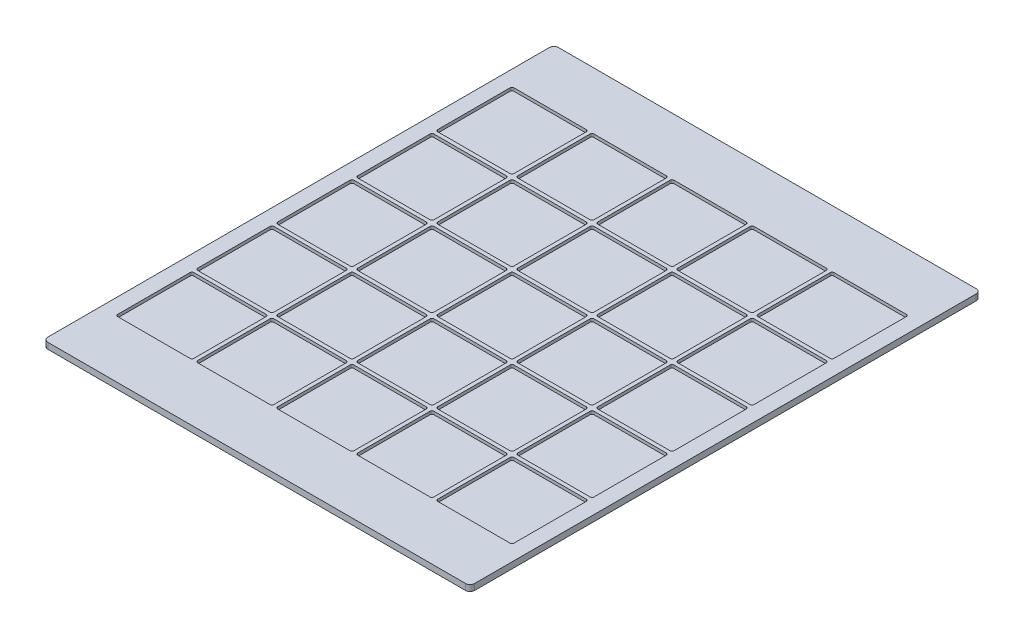
SolidWorks part; units mm, degrees
ref_plane "Front Plane" through (0, 0, 0) normal (0, 0, 1) x (1, 0, 0)
ref_plane "Top Plane" through (0, 0, 0) normal (0, 1, 0) x (1, 0, 0)
ref_plane "Right Plane" through (0, 0, 0) normal (1, 0, 0) x (0, 0, -1)
sketch "Sketch1" plane through (0, 0, 0) normal (0, 1, 0) x (1, 0, 0)
  line L0 (-193.675, 203.2) -> (-73.025, 203.2)
  line L1 (-327.025, 203.2) -> (-206.375, 203.2)
  line L2 (-330.2, 206.375) -> (-330.2, 327.025)
  line L3 (-327.025, 330.2) -> (-206.375, 330.2)
  line L4 (-203.2, 206.375) -> (-203.2, 327.025)
  line L5 (-330.2, 203.2) -> (-203.2, 330.2) construction
  line L6 (-330.2, 330.2) -> (-203.2, 203.2) construction
  line L7 (-196.85, 206.375) -> (-196.85, 327.025)
  line L8 (-193.675, 330.2) -> (-73.025, 330.2)
  line L9 (-69.85, 206.375) -> (-69.85, 327.025)
  line L10 (-196.85, 203.2) -> (-69.85, 330.2) construction
  line L11 (-196.85, 330.2) -> (-69.85, 203.2) construction
  line L12 (-60.325, 203.2) -> (60.325, 203.2)
  line L13 (-63.5, 206.375) -> (-63.5, 327.025)
  line L14 (-60.325, 330.2) -> (60.325, 330.2)
  line L15 (63.5, 206.375) -> (63.5, 327.025)
  line L16 (-63.5, 203.2) -> (63.5, 330.2) construction
  line L17 (-63.5, 330.2) -> (63.5, 203.2) construction
  line L18 (73.025, 203.2) -> (193.675, 203.2)
  line L19 (69.85, 206.375) -> (69.85, 327.025)
  line L20 (73.025, 330.2) -> (193.675, 330.2)
  line L21 (196.85, 206.375) -> (196.85, 327.025)
  line L22 (69.85, 203.2) -> (196.85, 330.2) construction
  line L23 (69.85, 330.2) -> (196.85, 203.2) construction
  line L24 (206.375, 203.2) -> (327.025, 203.2)
  line L25 (203.2, 206.375) -> (203.2, 327.025)
  line L26 (206.375, 330.2) -> (327.025, 330.2)
  line L27 (330.2, 206.375) -> (330.2, 327.025)
  line L28 (203.2, 203.2) -> (330.2, 330.2) construction
  line L29 (203.2, 330.2) -> (330.2, 203.2) construction
  line L30 (-193.675, 69.85) -> (-73.025, 69.85)
  line L31 (-196.85, 73.025) -> (-196.85, 193.675)
  line L32 (-193.675, 196.85) -> (-73.025, 196.85)
  line L33 (-69.85, 73.025) -> (-69.85, 193.675)
  line L34 (-196.85, 69.85) -> (-69.85, 196.85) construction
  line L35 (-196.85, 196.85) -> (-69.85, 69.85) construction
  line L36 (-60.325, 69.85) -> (60.325, 69.85)
  line L37 (-63.5, 73.025) -> (-63.5, 193.675)
  line L38 (-60.325, 196.85) -> (60.325, 196.85)
  line L39 (63.5, 73.025) -> (63.5, 193.675)
  line L40 (-63.5, 69.85) -> (63.5, 196.85) construction
  line L41 (-63.5, 196.85) -> (63.5, 69.85) construction
  line L42 (73.025, 69.85) -> (193.675, 69.85)
  line L43 (69.85, 73.025) -> (69.85, 193.675)
  line L44 (73.025, 196.85) -> (193.675, 196.85)
  line L45 (196.85, 73.025) -> (196.85, 193.675)
  line L46 (69.85, 69.85) -> (196.85, 196.85) construction
  line L47 (69.85, 196.85) -> (196.85, 69.85) construction
  line L48 (206.375, 69.85) -> (327.025, 69.85)
  line L49 (203.2, 73.025) -> (203.2, 193.675)
  line L50 (206.375, 196.85) -> (327.025, 196.85)
  line L51 (330.2, 73.025) -> (330.2, 193.675)
  line L52 (203.2, 69.85) -> (330.2, 196.85) construction
  line L53 (203.2, 196.85) -> (330.2, 69.85) construction
  line L54 (-193.675, -63.5) -> (-73.025, -63.5)
  line L55 (-196.85, -60.325) -> (-196.85, 60.325)
  line L56 (-193.675, 63.5) -> (-73.025, 63.5)
  line L57 (-69.85, -60.325) -> (-69.85, 60.325)
  line L58 (-196.85, -63.5) -> (-69.85, 63.5) construction
  line L59 (-196.85, 63.5) -> (-69.85, -63.5) construction
  line L60 (-60.325, -63.5) -> (60.325, -63.5)
  line L61 (-63.5, -60.325) -> (-63.5, 60.325)
  line L62 (-60.325, 63.5) -> (60.325, 63.5)
  line L63 (63.5, -60.325) -> (63.5, 60.325)
  line L64 (-63.5, -63.5) -> (63.5, 63.5) construction
  line L65 (-63.5, 63.5) -> (63.5, -63.5) construction
  line L66 (73.025, -63.5) -> (193.675, -63.5)
  line L67 (69.85, -60.325) -> (69.85, 60.325)
  line L68 (73.025, 63.5) -> (193.675, 63.5)
  line L69 (196.85, -60.325) -> (196.85, 60.325)
  line L70 (69.85, -63.5) -> (196.85, 63.5) construction
  line L71 (69.85, 63.5) -> (196.85, -63.5) construction
  line L72 (206.375, -63.5) -> (327.025, -63.5)
  line L73 (203.2, -60.325) -> (203.2, 60.325)
  line L74 (206.375, 63.5) -> (327.025, 63.5)
  line L75 (330.2, -60.325) -> (330.2, 60.325)
  line L76 (203.2, -63.5) -> (330.2, 63.5) construction
  line L77 (203.2, 63.5) -> (330.2, -63.5) construction
  line L78 (-193.675, -196.85) -> (-73.025, -196.85)
  line L79 (-196.85, -193.675) -> (-196.85, -73.025)
  line L80 (-193.675, -69.85) -> (-73.025, -69.85)
  line L81 (-69.85, -193.675) -> (-69.85, -73.025)
  line L82 (-196.85, -196.85) -> (-69.85, -69.85) construction
  line L83 (-196.85, -69.85) -> (-69.85, -196.85) construction
  line L84 (-60.325, -196.85) -> (60.325, -196.85)
  line L85 (-63.5, -193.675) -> (-63.5, -73.025)
  line L86 (-60.325, -69.85) -> (60.325, -69.85)
  line L87 (63.5, -193.675) -> (63.5, -73.025)
  line L88 (-63.5, -196.85) -> (63.5, -69.85) construction
  line L89 (-63.5, -69.85) -> (63.5, -196.85) construction
  line L90 (73.025, -196.85) -> (193.675, -196.85)
  line L91 (69.85, -193.675) -> (69.85, -73.025)
  line L92 (73.025, -69.85) -> (193.675, -69.85)
  line L93 (196.85, -193.675) -> (196.85, -73.025)
  line L94 (69.85, -196.85) -> (196.85, -69.85) construction
  line L95 (69.85, -69.85) -> (196.85, -196.85) construction
  line L96 (206.375, -196.85) -> (327.025, -196.85)
  line L97 (203.2, -193.675) -> (203.2, -73.025)
  line L98 (206.375, -69.85) -> (327.025, -69.85)
  line L99 (330.2, -193.675) -> (330.2, -73.025)
  line L100 (203.2, -196.85) -> (330.2, -69.85) construction
  line L101 (203.2, -69.85) -> (330.2, -196.85) construction
  line L102 (-193.675, -330.2) -> (-73.025, -330.2)
  line L103 (-196.85, -327.025) -> (-196.85, -206.375)
  line L104 (-193.675, -203.2) -> (-73.025, -203.2)
  line L105 (-69.85, -327.025) -> (-69.85, -206.375)
  line L106 (-196.85, -330.2) -> (-69.85, -203.2) construction
  line L107 (-196.85, -203.2) -> (-69.85, -330.2) construction
  line L108 (-60.325, -330.2) -> (60.325, -330.2)
  line L109 (-63.5, -327.025) -> (-63.5, -206.375)
  line L110 (-60.325, -203.2) -> (60.325, -203.2)
  line L111 (63.5, -327.025) -> (63.5, -206.375)
  line L112 (-63.5, -330.2) -> (63.5, -203.2) construction
  line L113 (-63.5, -203.2) -> (63.5, -330.2) construction
  line L114 (73.025, -330.2) -> (193.675, -330.2)
  line L115 (69.85, -327.025) -> (69.85, -206.375)
  line L116 (73.025, -203.2) -> (193.675, -203.2)
  line L117 (196.85, -327.025) -> (196.85, -206.375)
  line L118 (69.85, -330.2) -> (196.85, -203.2) construction
  line L119 (69.85, -203.2) -> (196.85, -330.2) construction
  line L120 (206.375, -330.2) -> (327.025, -330.2)
  line L121 (203.2, -327.025) -> (203.2, -206.375)
  line L122 (206.375, -203.2) -> (327.025, -203.2)
  line L123 (330.2, -327.025) -> (330.2, -206.375)
  line L124 (203.2, -330.2) -> (330.2, -203.2) construction
  line L125 (203.2, -203.2) -> (330.2, -330.2) construction
  line L126 (-327.025, 69.85) -> (-206.375, 69.85)
  line L127 (-330.2, 73.025) -> (-330.2, 193.675)
  line L128 (-327.025, 196.85) -> (-206.375, 196.85)
  line L129 (-203.2, 73.025) -> (-203.2, 193.675)
  line L130 (-330.2, 69.85) -> (-203.2, 196.85) construction
  line L131 (-330.2, 196.85) -> (-203.2, 69.85) construction
  line L132 (-327.025, -63.5) -> (-206.375, -63.5)
  line L133 (-330.2, -60.325) -> (-330.2, 60.325)
  line L134 (-327.025, 63.5) -> (-206.375, 63.5)
  line L135 (-203.2, -60.325) -> (-203.2, 60.325)
  line L136 (-330.2, -63.5) -> (-203.2, 63.5) construction
  line L137 (-330.2, 63.5) -> (-203.2, -63.5) construction
  line L138 (-327.025, -196.85) -> (-206.375, -196.85)
  line L139 (-330.2, -193.675) -> (-330.2, -73.025)
  line L140 (-327.025, -69.85) -> (-206.375, -69.85)
  line L141 (-203.2, -193.675) -> (-203.2, -73.025)
  line L142 (-330.2, -196.85) -> (-203.2, -69.85) construction
  line L143 (-330.2, -69.85) -> (-203.2, -196.85) construction
  line L144 (-327.025, -330.2) -> (-206.375, -330.2)
  line L145 (-330.2, -327.025) -> (-330.2, -206.375)
  line L146 (-327.025, -203.2) -> (-206.375, -203.2)
  line L147 (-203.2, -327.025) -> (-203.2, -206.375)
  line L148 (-330.2, -330.2) -> (-203.2, -203.2) construction
  line L149 (-330.2, -203.2) -> (-203.2, -330.2) construction
  line L151 (-355.6, 425.45) -> (355.6, 425.45)
  line L152 (-355.6, 425.45) -> (-355.6, -425.45)
  line L153 (-355.6, -425.45) -> (355.6, -425.45)
  line L154 (355.6, 425.45) -> (355.6, -425.45)
  arc A0 (-206.375, 330.2) -> (-203.2, 327.025) centre (-206.375, 327.025) cw
  arc A1 (-206.375, 203.2) -> (-203.2, 206.375) centre (-206.375, 206.375) ccw
  arc A2 (-327.025, 203.2) -> (-330.2, 206.375) centre (-327.025, 206.375) cw
  arc A3 (-330.2, 327.025) -> (-327.025, 330.2) centre (-327.025, 327.025) cw
  arc A4 (-73.025, 330.2) -> (-69.85, 327.025) centre (-73.025, 327.025) cw
  arc A5 (-73.025, 203.2) -> (-69.85, 206.375) centre (-73.025, 206.375) ccw
  arc A6 (-193.675, 203.2) -> (-196.85, 206.375) centre (-193.675, 206.375) cw
  arc A7 (-196.85, 327.025) -> (-193.675, 330.2) centre (-193.675, 327.025) cw
  arc A8 (60.325, 330.2) -> (63.5, 327.025) centre (60.325, 327.025) cw
  arc A9 (60.325, 203.2) -> (63.5, 206.375) centre (60.325, 206.375) ccw
  arc A10 (-60.325, 203.2) -> (-63.5, 206.375) centre (-60.325, 206.375) cw
  arc A11 (-63.5, 327.025) -> (-60.325, 330.2) centre (-60.325, 327.025) cw
  arc A12 (193.675, 330.2) -> (196.85, 327.025) centre (193.675, 327.025) cw
  arc A13 (193.675, 203.2) -> (196.85, 206.375) centre (193.675, 206.375) ccw
  arc A14 (73.025, 203.2) -> (69.85, 206.375) centre (73.025, 206.375) cw
  arc A15 (69.85, 327.025) -> (73.025, 330.2) centre (73.025, 327.025) cw
  arc A16 (327.025, 330.2) -> (330.2, 327.025) centre (327.025, 327.025) cw
  arc A17 (327.025, 203.2) -> (330.2, 206.375) centre (327.025, 206.375) ccw
  arc A18 (206.375, 203.2) -> (203.2, 206.375) centre (206.375, 206.375) cw
  arc A19 (203.2, 327.025) -> (206.375, 330.2) centre (206.375, 327.025) cw
  arc A20 (-73.025, 196.85) -> (-69.85, 193.675) centre (-73.025, 193.675) cw
  arc A21 (-73.025, 69.85) -> (-69.85, 73.025) centre (-73.025, 73.025) ccw
  arc A22 (-193.675, 69.85) -> (-196.85, 73.025) centre (-193.675, 73.025) cw
  arc A23 (-196.85, 193.675) -> (-193.675, 196.85) centre (-193.675, 193.675) cw
  arc A24 (60.325, 196.85) -> (63.5, 193.675) centre (60.325, 193.675) cw
  arc A25 (60.325, 69.85) -> (63.5, 73.025) centre (60.325, 73.025) ccw
  arc A26 (-60.325, 69.85) -> (-63.5, 73.025) centre (-60.325, 73.025) cw
  arc A27 (-63.5, 193.675) -> (-60.325, 196.85) centre (-60.325, 193.675) cw
  arc A28 (193.675, 196.85) -> (196.85, 193.675) centre (193.675, 193.675) cw
  arc A29 (193.675, 69.85) -> (196.85, 73.025) centre (193.675, 73.025) ccw
  arc A30 (73.025, 69.85) -> (69.85, 73.025) centre (73.025, 73.025) cw
  arc A31 (69.85, 193.675) -> (73.025, 196.85) centre (73.025, 193.675) cw
  arc A32 (327.025, 196.85) -> (330.2, 193.675) centre (327.025, 193.675) cw
  arc A33 (327.025, 69.85) -> (330.2, 73.025) centre (327.025, 73.025) ccw
  arc A34 (206.375, 69.85) -> (203.2, 73.025) centre (206.375, 73.025) cw
  arc A35 (203.2, 193.675) -> (206.375, 196.85) centre (206.375, 193.675) cw
  arc A36 (-73.025, 63.5) -> (-69.85, 60.325) centre (-73.025, 60.325) cw
  arc A37 (-73.025, -63.5) -> (-69.85, -60.325) centre (-73.025, -60.325) ccw
  arc A38 (-193.675, -63.5) -> (-196.85, -60.325) centre (-193.675, -60.325) cw
  arc A39 (-196.85, 60.325) -> (-193.675, 63.5) centre (-193.675, 60.325) cw
  arc A40 (60.325, 63.5) -> (63.5, 60.325) centre (60.325, 60.325) cw
  arc A41 (60.325, -63.5) -> (63.5, -60.325) centre (60.325, -60.325) ccw
  arc A42 (-60.325, -63.5) -> (-63.5, -60.325) centre (-60.325, -60.325) cw
  arc A43 (-63.5, 60.325) -> (-60.325, 63.5) centre (-60.325, 60.325) cw
  arc A44 (193.675, 63.5) -> (196.85, 60.325) centre (193.675, 60.325) cw
  arc A45 (193.675, -63.5) -> (196.85, -60.325) centre (193.675, -60.325) ccw
  arc A46 (73.025, -63.5) -> (69.85, -60.325) centre (73.025, -60.325) cw
  arc A47 (69.85, 60.325) -> (73.025, 63.5) centre (73.025, 60.325) cw
  arc A48 (327.025, 63.5) -> (330.2, 60.325) centre (327.025, 60.325) cw
  arc A49 (327.025, -63.5) -> (330.2, -60.325) centre (327.025, -60.325) ccw
  arc A50 (206.375, -63.5) -> (203.2, -60.325) centre (206.375, -60.325) cw
  arc A51 (203.2, 60.325) -> (206.375, 63.5) centre (206.375, 60.325) cw
  arc A52 (-73.025, -69.85) -> (-69.85, -73.025) centre (-73.025, -73.025) cw
  arc A53 (-73.025, -196.85) -> (-69.85, -193.675) centre (-73.025, -193.675) ccw
  arc A54 (-193.675, -196.85) -> (-196.85, -193.675) centre (-193.675, -193.675) cw
  arc A55 (-196.85, -73.025) -> (-193.675, -69.85) centre (-193.675, -73.025) cw
  arc A56 (60.325, -69.85) -> (63.5, -73.025) centre (60.325, -73.025) cw
  arc A57 (60.325, -196.85) -> (63.5, -193.675) centre (60.325, -193.675) ccw
  arc A58 (-60.325, -196.85) -> (-63.5, -193.675) centre (-60.325, -193.675) cw
  arc A59 (-63.5, -73.025) -> (-60.325, -69.85) centre (-60.325, -73.025) cw
  arc A60 (193.675, -69.85) -> (196.85, -73.025) centre (193.675, -73.025) cw
  arc A61 (193.675, -196.85) -> (196.85, -193.675) centre (193.675, -193.675) ccw
  arc A62 (73.025, -196.85) -> (69.85, -193.675) centre (73.025, -193.675) cw
  arc A63 (69.85, -73.025) -> (73.025, -69.85) centre (73.025, -73.025) cw
  arc A64 (327.025, -69.85) -> (330.2, -73.025) centre (327.025, -73.025) cw
  arc A65 (327.025, -196.85) -> (330.2, -193.675) centre (327.025, -193.675) ccw
  arc A66 (206.375, -196.85) -> (203.2, -193.675) centre (206.375, -193.675) cw
  arc A67 (203.2, -73.025) -> (206.375, -69.85) centre (206.375, -73.025) cw
  arc A68 (-73.025, -203.2) -> (-69.85, -206.375) centre (-73.025, -206.375) cw
  arc A69 (-73.025, -330.2) -> (-69.85, -327.025) centre (-73.025, -327.025) ccw
  arc A70 (-193.675, -330.2) -> (-196.85, -327.025) centre (-193.675, -327.025) cw
  arc A71 (-196.85, -206.375) -> (-193.675, -203.2) centre (-193.675, -206.375) cw
  arc A72 (60.325, -203.2) -> (63.5, -206.375) centre (60.325, -206.375) cw
  arc A73 (60.325, -330.2) -> (63.5, -327.025) centre (60.325, -327.025) ccw
  arc A74 (-60.325, -330.2) -> (-63.5, -327.025) centre (-60.325, -327.025) cw
  arc A75 (-63.5, -206.375) -> (-60.325, -203.2) centre (-60.325, -206.375) cw
  arc A76 (193.675, -203.2) -> (196.85, -206.375) centre (193.675, -206.375) cw
  arc A77 (193.675, -330.2) -> (196.85, -327.025) centre (193.675, -327.025) ccw
  arc A78 (73.025, -330.2) -> (69.85, -327.025) centre (73.025, -327.025) cw
  arc A79 (69.85, -206.375) -> (73.025, -203.2) centre (73.025, -206.375) cw
  arc A80 (327.025, -203.2) -> (330.2, -206.375) centre (327.025, -206.375) cw
  arc A81 (327.025, -330.2) -> (330.2, -327.025) centre (327.025, -327.025) ccw
  arc A82 (206.375, -330.2) -> (203.2, -327.025) centre (206.375, -327.025) cw
  arc A83 (203.2, -206.375) -> (206.375, -203.2) centre (206.375, -206.375) cw
  arc A84 (-206.375, 196.85) -> (-203.2, 193.675) centre (-206.375, 193.675) cw
  arc A85 (-206.375, 69.85) -> (-203.2, 73.025) centre (-206.375, 73.025) ccw
  arc A86 (-327.025, 69.85) -> (-330.2, 73.025) centre (-327.025, 73.025) cw
  arc A87 (-330.2, 193.675) -> (-327.025, 196.85) centre (-327.025, 193.675) cw
  arc A88 (-206.375, 63.5) -> (-203.2, 60.325) centre (-206.375, 60.325) cw
  arc A89 (-206.375, -63.5) -> (-203.2, -60.325) centre (-206.375, -60.325) ccw
  arc A90 (-327.025, -63.5) -> (-330.2, -60.325) centre (-327.025, -60.325) cw
  arc A91 (-330.2, 60.325) -> (-327.025, 63.5) centre (-327.025, 60.325) cw
  arc A92 (-206.375, -69.85) -> (-203.2, -73.025) centre (-206.375, -73.025) cw
  arc A93 (-206.375, -196.85) -> (-203.2, -193.675) centre (-206.375, -193.675) ccw
  arc A94 (-327.025, -196.85) -> (-330.2, -193.675) centre (-327.025, -193.675) cw
  arc A95 (-330.2, -73.025) -> (-327.025, -69.85) centre (-327.025, -73.025) cw
  arc A96 (-206.375, -203.2) -> (-203.2, -206.375) centre (-206.375, -206.375) cw
  arc A97 (-206.375, -330.2) -> (-203.2, -327.025) centre (-206.375, -327.025) ccw
  arc A98 (-327.025, -330.2) -> (-330.2, -327.025) centre (-327.025, -327.025) cw
  arc A99 (-330.2, -206.375) -> (-327.025, -203.2) centre (-327.025, -206.375) cw
  point P0 (0, 0)
  point P18 (0, 0)
  point P19 (0, 0)
  point P21 (133.35, 0)
  point P38 (266.7, 0)
  point P55 (400.05, 0)
  point P72 (533.4, 0)
  point P89 (133.35, -133.35)
  point P106 (266.7, -133.35)
  point P123 (400.05, -133.35)
  point P140 (533.4, -133.35)
  point P157 (133.35, -266.7)
  point P174 (266.7, -266.7)
  point P191 (400.05, -266.7)
  point P208 (533.4, -266.7)
  point P225 (133.35, -400.05)
  point P242 (266.7, -400.05)
  point P259 (400.05, -400.05)
  point P276 (533.4, -400.05)
  point P293 (133.35, -533.4)
  point P310 (266.7, -533.4)
  point P327 (400.05, -533.4)
  point P344 (533.4, -533.4)
  point P361 (0, -133.35)
  point P378 (0, -266.7)
  point P395 (0, -400.05)
  point P412 (0, -533.4)
  dimension "D3" = 3.175
  dimension "D1" = 127
  dimension "D2" = 127
  dimension "D6" = 95.25
  dimension "D7" = 25.4
  dimension "D8" = 25.4
  dimension "D9" = 95.25
  dimension "D11" = 6.35
  dimension "D12" = 6.35
  dimension "D4" = 5
  dimension "D5" = 5
extrude "Boss-Extrude1" add sketch "Sketch1" along normal blind 5.08
sketch "Sketch2" plane through (0, 0, 0) normal (0, -1, 0) x (1, 0, 0)
  line L0 (-355.6, 425.45) -> (355.6, 425.45) construction
  line L1 (-355.6, -425.45) -> (-355.6, 425.45) construction
  line L2 (-355.6, 425.45) -> (355.6, 425.45)
  line L3 (-355.6, -425.45) -> (-355.6, 425.45)
  line L4 (-355.6, -425.45) -> (355.6, -425.45) construction
  line L5 (-355.6, -425.45) -> (355.6, -425.45)
  line L6 (355.6, -425.45) -> (355.6, 425.45) construction
  line L7 (355.6, -425.45) -> (355.6, 425.45)
extrude "Boss-Extrude2" add sketch "Sketch2" along normal blind 5.08
sketch "Sketch3" plane through (0, 0, 0) normal (0, 1, 0) x (1, 0, 0)
  line L0 (-330.2, 69.85) -> (-203.2, 196.85) construction
  line L1 (-330.2, 63.5) -> (-203.2, -63.5) construction
  line L2 (-330.2, -330.2) -> (-203.2, -203.2) construction
  line L3 (-196.85, -69.85) -> (-69.85, -196.85) construction
  line L4 (-63.5, 203.2) -> (63.5, 330.2) construction
  line L5 (-63.5, 69.85) -> (63.5, 196.85) construction
  line L6 (-63.5, 63.5) -> (63.5, -63.5) construction
  line L7 (-63.5, -69.85) -> (63.5, -196.85) construction
  line L8 (69.85, 196.85) -> (196.85, 69.85) construction
  line L9 (203.2, -63.5) -> (330.2, 63.5) construction
  line L10 (203.2, -69.85) -> (330.2, -196.85) construction
  line L11 (203.2, -330.2) -> (330.2, -203.2) construction
  point P0 (0, 0)
  point P1 (-266.7, 133.35)
  point P3 (-266.7, 0)
  point P6 (0, -400.05)
  point P9 (-266.7, -266.7)
  point P11 (133.35, -533.4)
  point P14 (-133.35, -133.35)
  point P16 (133.35, -266.7)
  point P19 (133.35, -133.35)
  point P21 (133.35, 0)
  point P23 (0, 266.7)
  point P25 (0, 133.35)
  point P28 (0, 0)
  point P31 (0, -133.35)
  point P34 (266.7, -533.4)
  point P37 (400.05, -533.4)
  point P39 (400.05, -400.05)
  point P41 (400.05, -266.7)
  point P43 (133.35, 133.35)
  point P45 (400.05, 0)
  point P48 (533.4, 0)
  point P50 (533.4, -133.35)
  point P52 (266.7, 0)
  point P54 (266.7, -133.35)
  point P57 (266.7, -266.7)
ref_plane "Plane1" through (0, 0, 0) normal (1, 0, 0) x (0, 0, -1)
fillet "Fillet1" radius 7.62 4 edges at (-355.6, 0, -425.45) (355.6, 0, -425.45) (355.6, 0, 425.45) (-355.6, 0, 425.45)
sketch "Sketch4" plane through (0, 5.08, 0) normal (0, 1, 0) x (1, 0, 0)
  line L0 (-350.3859, 0) -> (-355.6, 0) construction
  line L1 (0, 425.45) -> (0, -761.9951) construction
  line L2 (-355.6, 417.83) -> (-355.6, -417.83) construction
  line L3 (350.3859, 0) -> (355.6, 0) construction
  line L4 (-330.2, -10.4282) -> (-340.6282, 10.4282)
  line L5 (-330.2, -60.325) -> (-330.2, 60.325) construction
  line L6 (-347.98, 425.45) -> (347.98, 425.45) construction
  line L7 (-345.1718, 10.4282) -> (-355.6, -10.4282)
  line L8 (345.1718, 10.4282) -> (355.6, -10.4282)
  line L9 (330.2, -10.4282) -> (340.6282, 10.4282)
  line L10 (-203.2, 0) -> (203.2, 0)
  line L11 (-203.2, -60.325) -> (-203.2, 60.325) construction
  line L12 (203.2, -60.325) -> (203.2, 60.325) construction
  line L13 (203.2, 0) -> (330.2, -10.4282)
  line L14 (-203.2, 0) -> (-330.2, -10.4282)
  arc A0 (345.1718, 10.4282) -> (340.6282, 10.4282) centre (342.9, 9.2922) ccw
  arc A1 (-340.6282, 10.4282) -> (-345.1718, 10.4282) centre (-342.9, 9.2922) ccw
  point P13 (-350.3859, 0)
  point P27 (342.9, 14.9718)
  point P30 (-342.9, 14.9718)
  dimension "D2" = 2.54
  dimension "D1" = 25.4
split line "Split Line1" [suppressed]
equation "\"D8@Sketch1\"=\"D7@Sketch1\""
equation "\"D9@Sketch1\"=\"D6@Sketch1\""
equation "\"D12@Sketch1\"=\"D11@Sketch1\""
